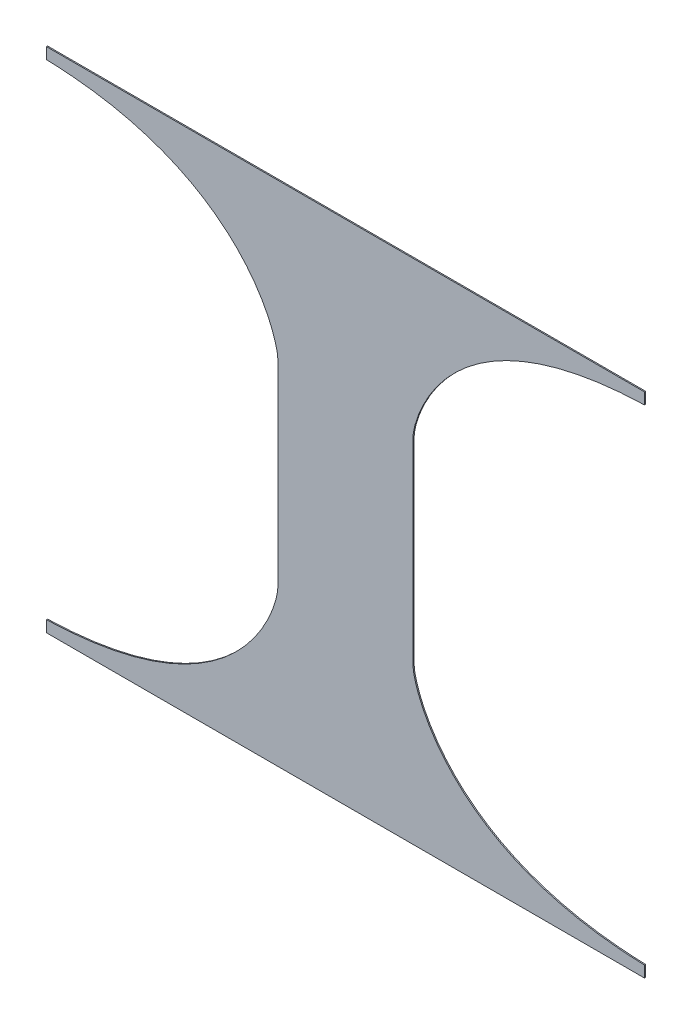
SolidWorks part; units mm, degrees
material "Beech"
ref_plane "Front" through (0, 0, 0) normal (0, 0, 1) x (1, 0, 0)
ref_plane "Top" through (0, 0, 0) normal (0, 1, 0) x (1, 0, 0)
ref_plane "Right" through (0, 0, 0) normal (1, 0, 0) x (0, 0, -1)
sketch "Sketch1" plane through (0, 0, 0) normal (0, 0, 1) x (1, 0, 0)
  line L1 (-673.1, -571.5) -> (673.1, -571.5)
  line L2 (-673.1, -571.5) -> (-673.1, 571.5)
  line L3 (-673.1, 571.5) -> (673.1, 571.5)
  line L4 (673.1, -571.5) -> (673.1, 571.5)
  line L5 (-673.1, -571.5) -> (673.1, 571.5) construction
  line L6 (-673.1, 571.5) -> (673.1, -571.5) construction
  point P0 (0, 0)
  dimension "D1" = 1346.2
  dimension "D2" = 1143
extrude "Boss-Extrude1" add sketch "Sketch1" along normal mid plane 2.54
sketch "Sketch2" plane through (0, 0, 1.27) normal (0, 0, 1) x (1, 0, 0)
  line L0 (673.1, 571.5) -> (-673.1, 571.5) construction
  line L1 (-152.4, -571.5) -> (152.4, -571.5) construction
  line L2 (-152.4, -571.5) -> (-152.4, 571.5) construction
  line L3 (-152.4, 571.5) -> (152.4, 571.5) construction
  line L4 (152.4, -571.5) -> (152.4, 571.5) construction
  line L5 (-152.4, -571.5) -> (152.4, 571.5) construction
  line L6 (-152.4, 571.5) -> (152.4, -571.5) construction
  line L7 (-673.1, 0) -> (673.1, 0) construction
  line L8 (-673.1, 571.5) -> (-673.1, -571.5) construction
  line L9 (673.1, -571.5) -> (673.1, 571.5) construction
  line L10 (-673.1, 546.1) -> (-673.1, -546.1)
  line L11 (-152.4, 224.4951) -> (-152.4, -224.4951)
  line L12 (0, 571.5) -> (0, -571.5) construction
  line L13 (673.1, 546.1) -> (673.1, -546.1)
  line L14 (152.4, 224.4951) -> (152.4, -224.4951)
  spline S0 degree 3 poles (-152.4, 224.4951) (-152.4, 258.7047) (-224.0532, 532.7777) (-673.1, 546.1) knots 0 0 0 0 1 1 1 1
  spline S1 degree 3 poles (-152.4, -224.4951) (-152.4, -258.7047) (-224.0532, -532.7777) (-673.1, -546.1) knots 0 0 0 0 1 1 1 1
  spline S2 degree 3 poles (152.4, 224.4951) (152.4, 258.7047) (224.0532, 532.7777) (673.1, 546.1) knots 0 0 0 0 1 1 1 1
  spline S3 degree 3 poles (152.4, -224.4951) (152.4, -258.7047) (224.0532, -532.7777) (673.1, -546.1) knots 0 0 0 0 1 1 1 1
  point P0 (0, 0)
  dimension "D2" = 25.4
  dimension "D1" = 304.8
extrude "Cut-Extrude1" cut sketch "Sketch2" against normal through all
